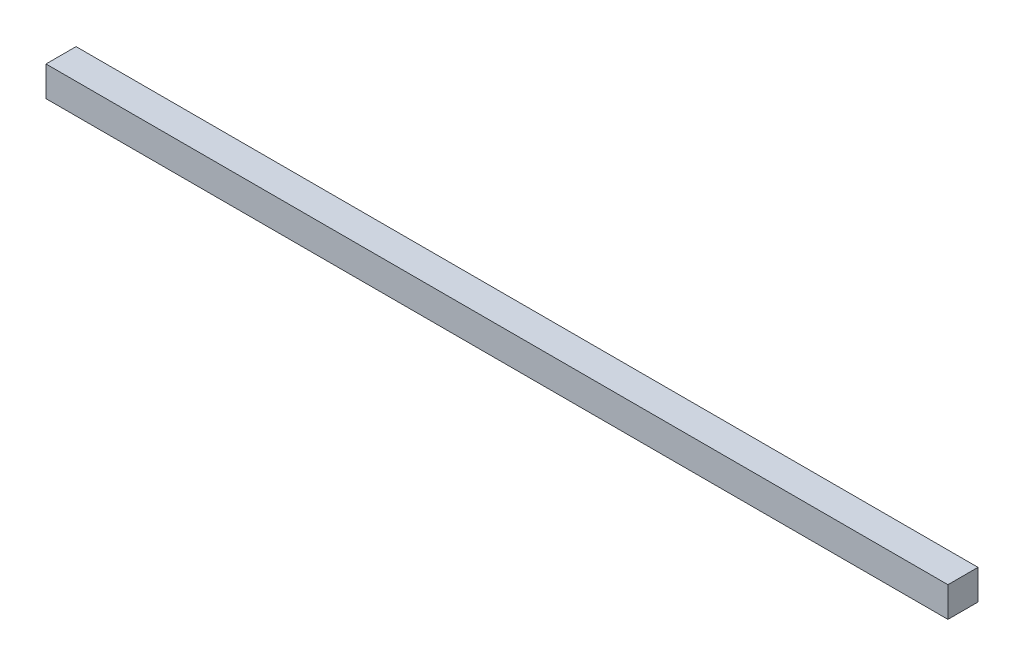
SolidWorks part; units mm, degrees
ref_plane "Front Plane" through (0, 0, 0) normal (0, 0, 1) x (1, 0, 0)
ref_plane "Top Plane" through (0, 0, 0) normal (0, 1, 0) x (1, 0, 0)
ref_plane "Right Plane" through (0, 0, 0) normal (1, 0, 0) x (0, 0, -1)
sketch "Sketch1" plane through (0, 0, 0) normal (0, 1, 0) x (1, 0, 0)
  line L1 (0, 0) -> (300, 0) construction
  line L2 (300, -10) -> (300, 10)
  line L4 (0, 27.2438) -> (0, -37.4428) construction
  line L6 (300, 10) -> (-300, 10)
  line L7 (300, -10) -> (-300, -10)
  line L8 (-300, -10) -> (-300, 10)
  point P10 (0, -10)
  point P11 (0, -10)
  point P12 (0, 10)
  point P13 (0, 10)
  dimension "D1" = 10
  dimension "D2" = 10
  dimension "D3" = 300
  dimension "D4" = 90
extrude "Boss-Extrude1" add sketch "Sketch1" along normal blind 20
